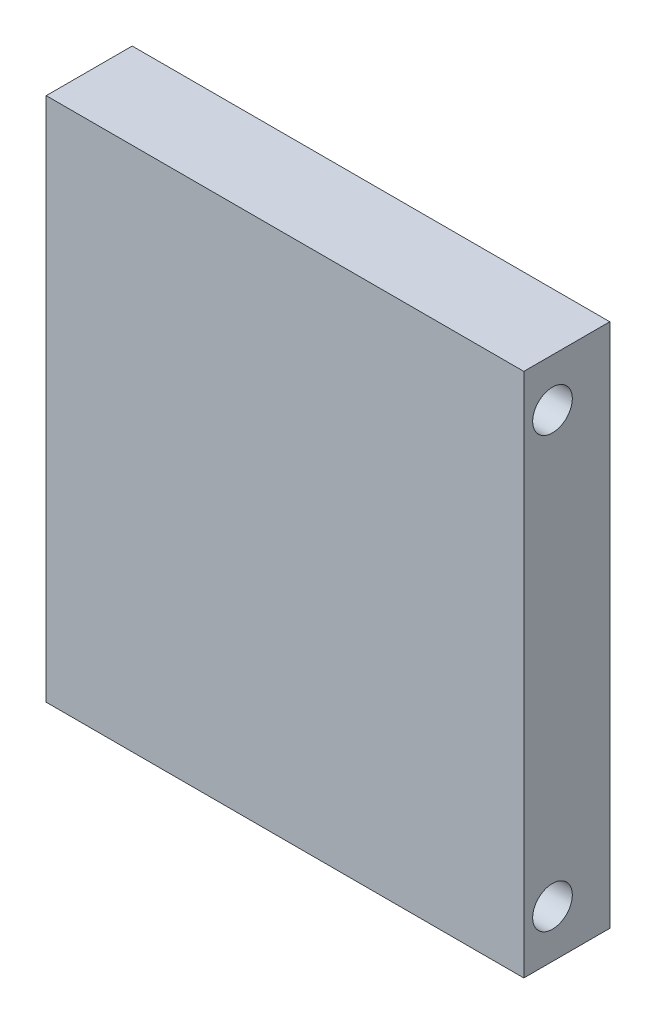
SolidWorks part; units mm, degrees
ref_plane "Front Plane" through (0, 0, 0) normal (0, 0, 1) x (1, 0, 0)
ref_plane "Top Plane" through (0, 0, 0) normal (0, 1, 0) x (1, 0, 0)
ref_plane "Right Plane" through (0, 0, 0) normal (1, 0, 0) x (0, 0, -1)
sketch "Esboço1" plane through (0, 0, 0) normal (0, 0, 1) x (1, 0, 0)
  line L0 (0, 55) -> (0, -55) construction
  line L1 (-50, 55) -> (50, 55)
  line L2 (-50, 55) -> (-50, -55)
  line L3 (-50, -55) -> (50, -55)
  line L4 (50, 55) -> (50, -55)
  point P6 (0, 0)
  dimension "D1" = 100
  dimension "D2" = 110
extrude "Ressalto-extrusão1" add sketch "Esboço1" along normal blind 18
sketch "Esboço2" plane through (0, 0, 0) normal (0, 0, -1) x (-1, 0, 0)
  line L16 (50, 0) -> (-50, 0) construction
  line L17 (50, 55) -> (50, -55) construction
  line L18 (-50, -55) -> (-50, 55) construction
  line L19 (0, 55) -> (0, -55) construction
  line L20 (-34, -16) -> (-16, -16)
  line L21 (-34, -34) -> (-34, -16)
  line L22 (-16, -34) -> (-34, -34)
  line L23 (-16, -16) -> (-16, -34)
  line L24 (16, -16) -> (16, -34)
  line L25 (34, -16) -> (16, -16)
  line L26 (16, -34) -> (34, -34)
  line L27 (34, -34) -> (34, -16)
  line L28 (-50, 55) -> (50, 55) construction
  line L29 (50, -55) -> (-50, -55) construction
  line L30 (-34, 34) -> (-34, 16)
  line L31 (-16, 34) -> (-34, 34)
  line L32 (-16, 16) -> (-16, 34)
  line L33 (-34, 16) -> (-16, 16)
  line L34 (34, 16) -> (16, 16)
  line L35 (34, 34) -> (34, 16)
  line L36 (16, 34) -> (34, 34)
  line L37 (16, 16) -> (16, 34)
extrude "Ressalto-extrusão2" add sketch "Esboço2" along normal blind 10
sketch "Esboço3" plane through (-50, 0, 0) normal (-1, 0, 0) x (0, 0, 1)
  circle A2 centre (12, 45) radius 4.15
  circle A3 centre (12, 45) radius 4.15
  circle A5 centre (12, -45) radius 4.15
  circle A6 centre (12, -45) radius 4.15
  dimension "D1" = 0
  dimension "D2" = 0
extrude "Corte-extrusão1" cut sketch "Esboço3" against normal through all
